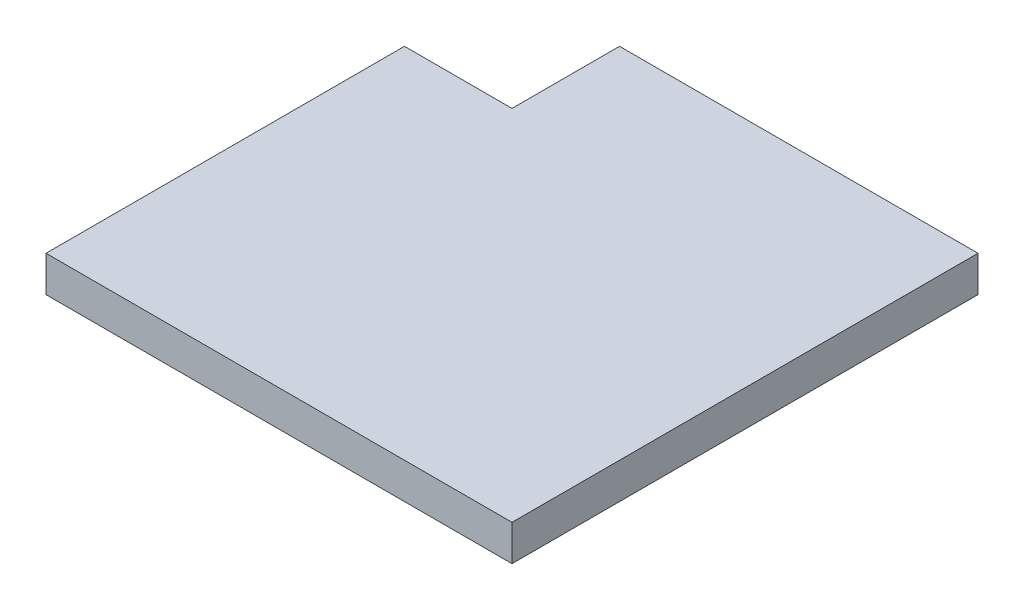
SolidWorks part; units mm, degrees
ref_plane "Front Plane" through (0, 0, 0) normal (0, 0, 1) x (1, 0, 0)
ref_plane "Top Plane" through (0, 0, 0) normal (0, 1, 0) x (1, 0, 0)
ref_plane "Right Plane" through (0, 0, 0) normal (1, 0, 0) x (0, 0, -1)
sketch "Sketch1" plane through (0, 0, 0) normal (0, 1, 0) x (1, 0, 0)
  line L0 (-65, 65) -> (65, -65) construction
  line L1 (-65, 65) -> (65, 65) construction
  line L2 (-65, 65) -> (-65, -65) construction
  line L3 (-65, -65) -> (65, -65) construction
  line L4 (65, 65) -> (65, -65) construction
  line L5 (-65, -65) -> (65, -65)
  line L6 (65, -65) -> (65, 65)
  line L7 (65, 65) -> (-35, 65)
  line L8 (-35, 65) -> (-35, 35)
  line L9 (-35, 35) -> (-65, 35)
  line L10 (-65, 35) -> (-65, -65)
  dimension "D1" = 130
  dimension "D2" = 130
  dimension "D3" = 100
  dimension "D4" = 100
extrude "Boss-Extrude1" add sketch "Sketch1" along normal blind 10
